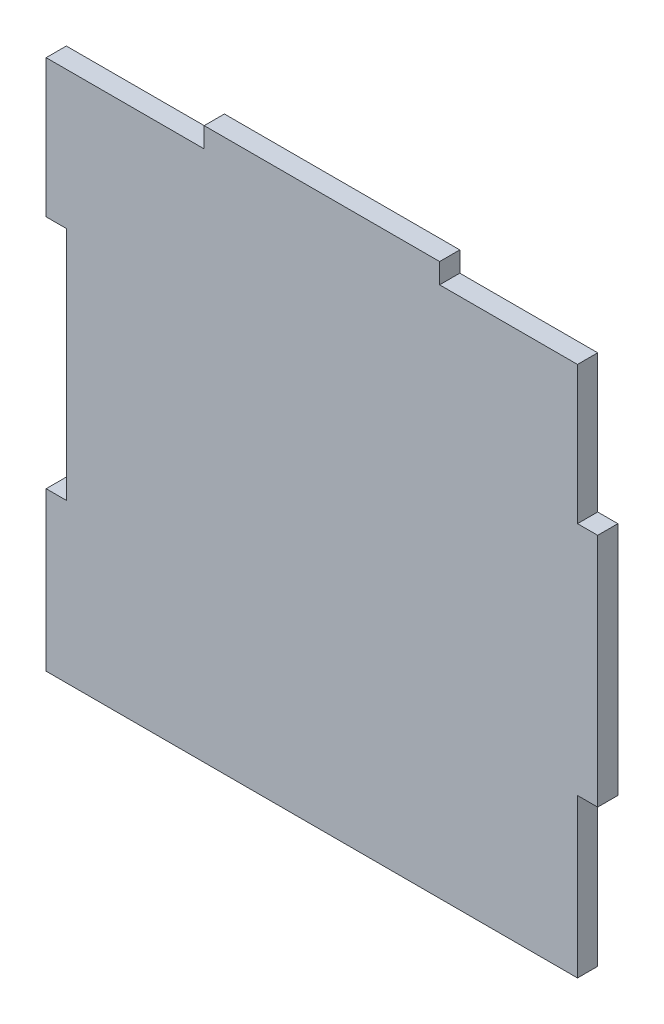
SolidWorks part; units mm, degrees
ref_plane "Front Plane" through (0, 0, 0) normal (0, 0, 1) x (1, 0, 0)
ref_plane "Top Plane" through (0, 0, 0) normal (0, 1, 0) x (1, 0, 0)
ref_plane "Right Plane" through (0, 0, 0) normal (1, 0, 0) x (0, 0, -1)
sketch "Sketch1" plane through (0, 0, 0) normal (0, 0, 1) x (1, 0, 0)
  line L0 (0, 38) -> (0, -39.5) construction
  line L5 (-38, 39.5) -> (-17.5, 39.5)
  line L6 (-38, 16) -> (-38, -16)
  line L24 (38, 39.5) -> (38, 19)
  line L26 (-41, -39.5) -> (38, -39.5)
  line L27 (-38, 0) -> (38, 0) construction
  line L28 (-17.5, 39.5) -> (-17.5, 42.5)
  line L29 (-17.5, 42.5) -> (17.5, 42.5)
  line L30 (17.5, 42.5) -> (17.5, 39.5)
  line L33 (-41, 19) -> (-41, 39.5)
  line L34 (-41, 39.5) -> (-38, 39.5)
  line L35 (-41, -19) -> (-41, -39.5)
  line L36 (38, -19) -> (38, -39.5)
  line L43 (41, 16) -> (41, -16)
  line L44 (-38, 16) -> (-38, 19)
  line L46 (17.5, 39.5) -> (38, 39.5)
  line L48 (-38, 19) -> (-41, 19)
  line L50 (-41, -19) -> (-41, -16)
  line L51 (-41, -16) -> (-38, -16)
  line L52 (38, -19) -> (38, -16)
  line L53 (38, -16) -> (41, -16)
  line L54 (41, 16) -> (41, 19)
  line L55 (41, 19) -> (38, 19)
  point P0 (0, 0)
  dimension "D1" = 79
  dimension "D2" = 76
  dimension "D3" = 3
  dimension "D4" = 35
  dimension "D5" = 3
  dimension "D6" = 76
  dimension "D7" = 35
  dimension "D8" = 3
  dimension "D9" = 3
  dimension "D10" = 3
  dimension "D11" = 3
  dimension "D12" = 35
  dimension "D13" = 0
  dimension "D14" = 20.5
extrude "Boss-Extrude1" add sketch "Sketch1" along normal blind 3
